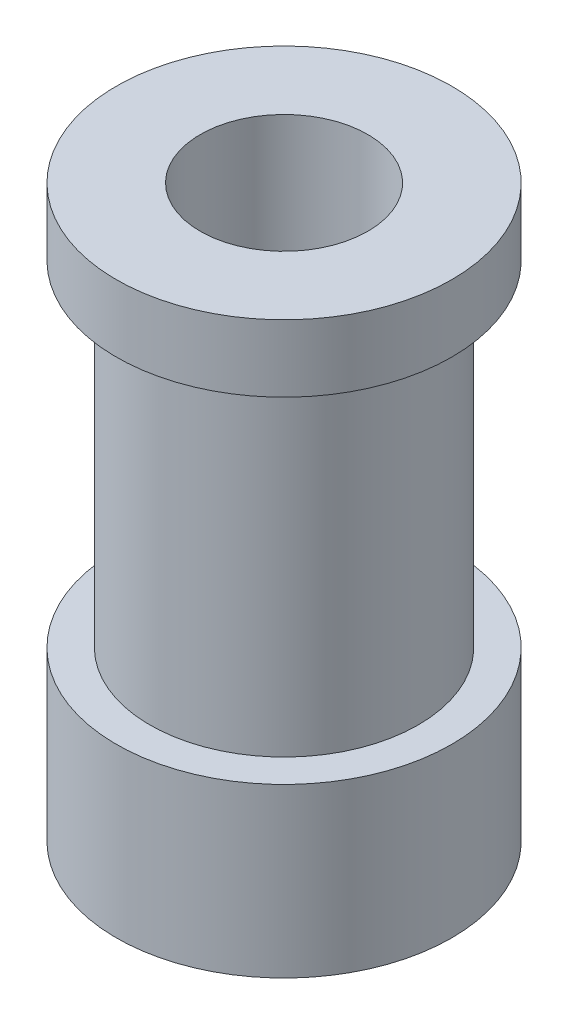
SolidWorks part; units mm, degrees
ref_plane "Front Plane" through (0, 0, 0) normal (0, 0, 1) x (1, 0, 0)
ref_plane "Top Plane" through (0, 0, 0) normal (0, 1, 0) x (1, 0, 0)
ref_plane "Right Plane" through (0, 0, 0) normal (1, 0, 0) x (0, 0, -1)
sketch "Sketch1" plane through (0, 0, 0) normal (0, 0, 1) x (1, 0, 0)
  line L0 (0, 0) -> (0, 17) construction
  line L1 (2.5, 0) -> (5, 0)
  line L2 (5, 0) -> (5, 5)
  line L3 (5, 5) -> (4, 5)
  line L4 (4, 5) -> (4, 15)
  line L5 (4, 15) -> (5, 15)
  line L6 (5, 15) -> (5, 17)
  line L7 (5, 17) -> (2.5, 17)
  line L8 (2.5, 17) -> (2.5, 0)
  dimension "D1" = 17
  dimension "D2" = 2.5
  dimension "D3" = 5
  dimension "D4" = 5
  dimension "D5" = 10
  dimension "D6" = 4
  dimension "D7" = 5
revolve "Revolve1" add sketch "Sketch1" angle 360 about L0
sketch "Sketch3" plane through (0, 0, 0) normal (0, 0, 1) x (1, 0, 0)
  line L0 (5, 0) -> (5, 5) construction
  circle A0 centre (0, 2.5) radius 1
  dimension "D1" = 2
  dimension "D2" = 2.5
  dimension "D3" = 5
extrude "Cut-Extrude1" cut sketch "Sketch3" against normal blind 10
sketch "Sketch4" plane through (0, 0, 0) normal (1, 0, 0) x (0, 0, -1)
  line L0 (-5, 5) -> (-5, 0) construction
  circle A0 centre (0, 2.5) radius 1
  dimension "D1" = 2
  dimension "D2" = 5
  dimension "D3" = 2.5
extrude "Cut-Extrude2" cut sketch "Sketch4" against normal blind 10
